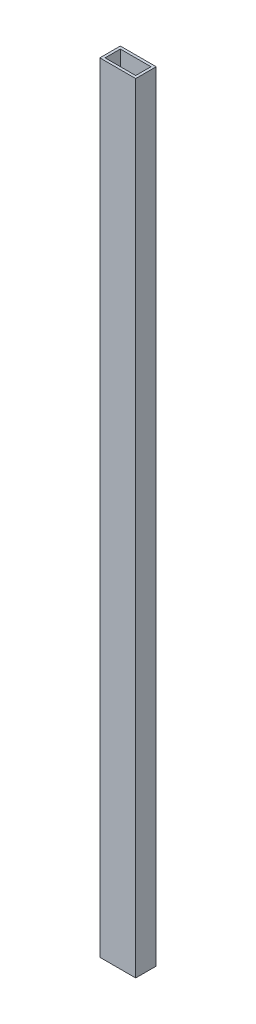
SolidWorks part; units mm, degrees
ref_plane "Front Plane" through (0, 0, 0) normal (0, 0, 1) x (1, 0, 0)
ref_plane "Top Plane" through (0, 0, 0) normal (0, 1, 0) x (1, 0, 0)
ref_plane "Right Plane" through (0, 0, 0) normal (1, 0, 0) x (0, 0, -1)
sketch "Sketch2" plane through (0, 0, 0) normal (0, 1, 0) x (1, 0, 0)
  line L1 (0, 0) -> (44.45, 0)
  line L2 (0, 0) -> (0, 25.4)
  line L3 (0, 25.4) -> (44.45, 25.4)
  line L4 (44.45, 0) -> (44.45, 25.4)
  dimension "D1" = 44.45
  dimension "1.75" = 25.4
extrude "Boss-Extrude2" add sketch "Sketch2" along normal blind 965.2
sketch "Sketch3" plane through (0, 965.2, 0) normal (0, 1, 0) x (1, 0, 0)
  line L3 (3.2385, 22.1615) -> (41.2115, 22.1615)
  line L5 (44.45, 25.4) -> (0, 25.4) construction
  line L6 (3.2385, 22.1615) -> (3.2385, 3.2385)
  line L7 (3.2385, 3.2385) -> (41.2115, 3.2385)
  line L8 (41.2115, 3.2385) -> (41.2115, 22.1615)
  line L9 (0, 25.4) -> (0, 0) construction
  line L10 (44.45, 0) -> (44.45, 25.4) construction
  line L11 (0, 0) -> (44.45, 0) construction
  dimension "D1" = 3.2385
  dimension "D2" = 3.2385
  dimension "D3" = 3.2385
  dimension "D4" = 3.2385
extrude "Cut-Extrude1" cut sketch "Sketch3" against normal blind 1092.2
